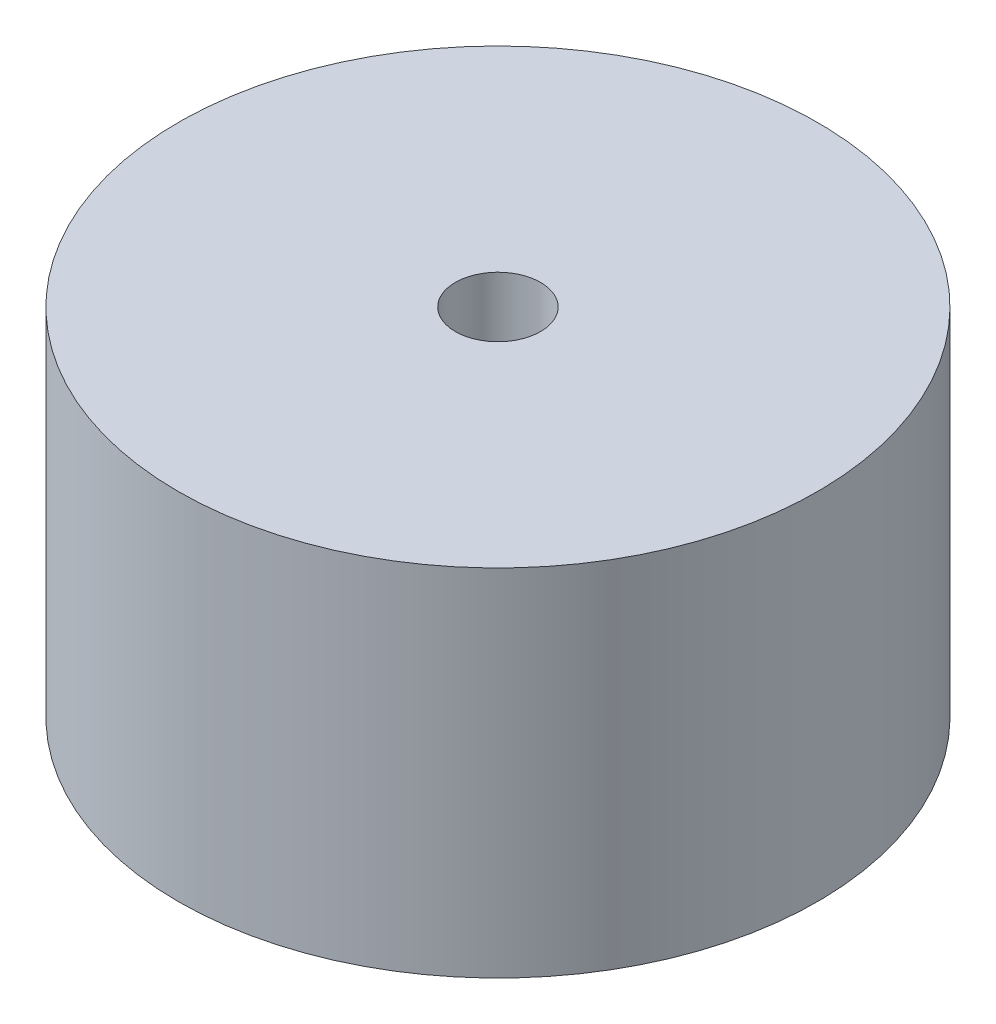
SolidWorks part; units mm, degrees
ref_plane "Front Plane" through (0, 0, 0) normal (0, 0, 1) x (1, 0, 0)
ref_plane "Top Plane" through (0, 0, 0) normal (0, 1, 0) x (1, 0, 0)
ref_plane "Right Plane" through (0, 0, 0) normal (1, 0, 0) x (0, 0, -1)
sketch "Sketch1" plane through (0, 0, 0) normal (0, 1, 0) x (1, 0, 0)
  circle A0 centre (0, 0) radius 45
extrude "Boss-Extrude1" add sketch "Sketch1" along normal blind 50
sketch "Sketch2" plane through (0, 0, 0) normal (1, 0, 0) x (0, 0, -1)
  line L0 (0, 50) -> (0, 0)
  line L1 (45, 50) -> (-45, 50) construction
  line L2 (0, 0) -> (-40, 0)
  line L3 (-45, 0) -> (45, 0) construction
  line L4 (-40, 0) -> (-40, 10)
  line L7 (-6, 50) -> (0, 50)
  line L8 (-40, 10) -> (-37, 10)
  line L9 (-37, 10) -> (-6, 41)
  line L10 (-6, 41) -> (-6, 50)
  dimension "D1" = 40
  dimension "D2" = 9
  dimension "D3" = 3
  dimension "D4" = 6
  dimension "D5" = 135
  dimension "D6" = 9
revolve "Cut-Revolve1" cut sketch "Sketch2" angle 360 about L0
